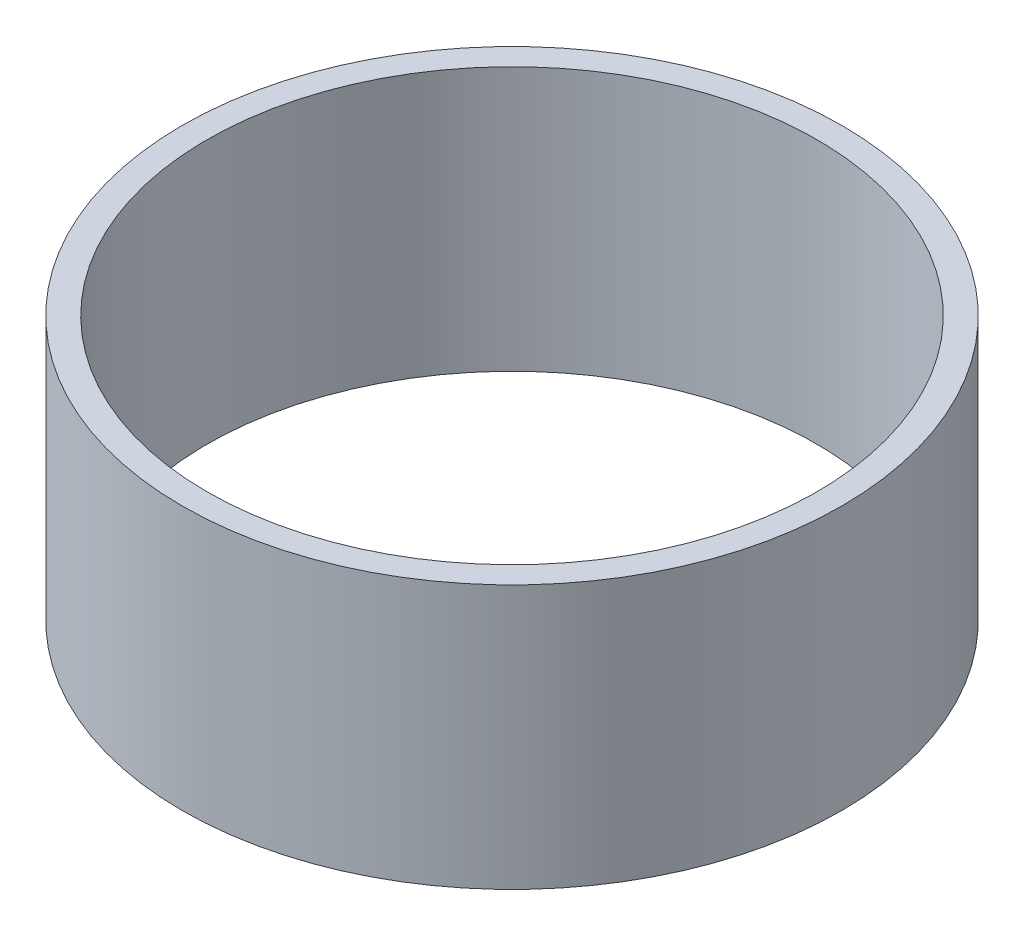
SolidWorks part; units mm, degrees
material "6061 Alloy"
ref_plane "Front Plane" through (0, 0, 0) normal (0, 0, 1) x (1, 0, 0)
ref_plane "Top Plane" through (0, 0, 0) normal (0, 1, 0) x (1, 0, 0)
ref_plane "Right Plane" through (0, 0, 0) normal (1, 0, 0) x (0, 0, -1)
sketch "Sketch1" plane through (0, 0, 0) normal (0, 1, 0) x (1, 0, 0)
  circle A0 centre (0, 0) radius 63.5
  circle A1 centre (0, 0) radius 58.7375
extrude "Extrude1" add sketch "Sketch1" along normal blind 50.8
